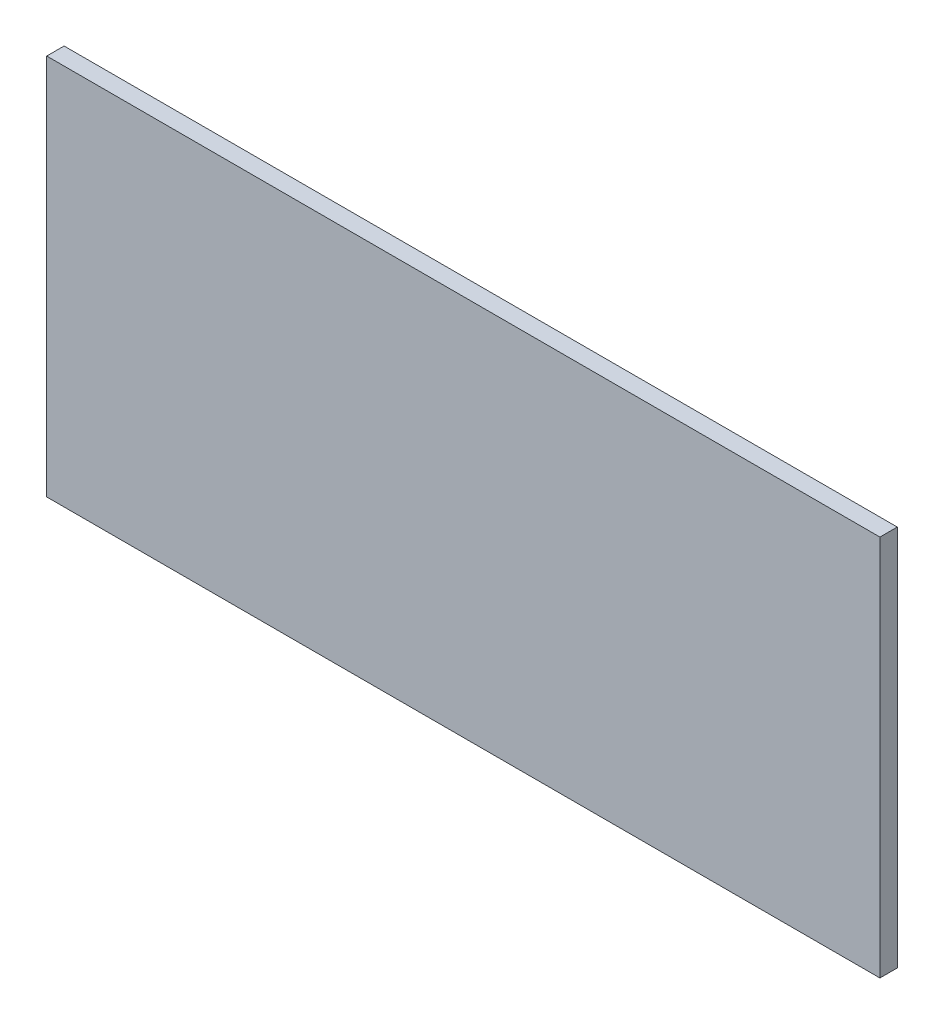
SolidWorks part; units mm, degrees
ref_plane "Front Plane" through (0, 0, 0) normal (0, 0, 1) x (1, 0, 0)
ref_plane "Top Plane" through (0, 0, 0) normal (0, 1, 0) x (1, 0, 0)
ref_plane "Right Plane" through (0, 0, 0) normal (1, 0, 0) x (0, 0, -1)
sketch "Sketch1" plane through (0, 0, 0) normal (0, 0, 1) x (1, 0, 0)
  line L1 (0, 0) -> (609.6, 0)
  line L2 (0, 0) -> (0, 279.4)
  line L3 (0, 279.4) -> (609.6, 279.4)
  line L4 (609.6, 0) -> (609.6, 279.4)
  dimension "D1" = 279.4
  dimension "D2" = 609.6
extrude "Boss-Extrude1" add sketch "Sketch1" along normal blind 12.7
